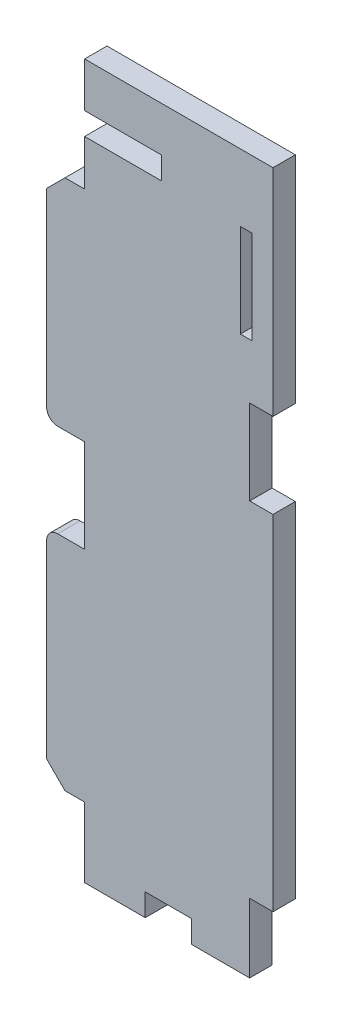
SolidWorks part; units mm, degrees
ref_plane "Front Plane" through (0, 0, 0) normal (0, 0, 1) x (1, 0, 0)
ref_plane "Top Plane" through (0, 0, 0) normal (0, 1, 0) x (1, 0, 0)
ref_plane "Right Plane" through (0, 0, 0) normal (1, 0, 0) x (0, 0, -1)
sketch "Model" plane through (0, 0, 0) normal (0, 0, 1) x (1, 0, 0)
  line L320 (15.6348, 91.059) -> (5.17, 91.059)
  line L321 (27.9538, 88.011) -> (26.379, 88.011)
  line L322 (27.649, 67.818) -> (27.649, 56.261)
  line L323 (30.824, 56.261) -> (27.649, 56.261)
  line L324 (30.824, 9.398) -> (30.824, 56.261)
  line L325 (27.649, 9.398) -> (30.824, 9.398)
  line L326 (27.649, 0) -> (27.649, 9.398)
  line L327 (27.649, 0) -> (19.7242, 0)
  line L328 (19.7242, 0) -> (19.7242, 3.048)
  line L329 (19.7242, 3.048) -> (13.425, 3.048)
  line L330 (13.425, 0) -> (13.425, 3.048)
  line L331 (13.425, 0) -> (5.17, 0)
  line L332 (5.17, 9.398) -> (5.17, 0)
  line L333 (15.6348, 88.011) -> (5.17, 88.011)
  line L334 (15.6348, 91.059) -> (15.6348, 88.011)
  line L335 (5.17, 97.155) -> (30.824, 97.155)
  line L336 (30.824, 67.818) -> (27.649, 67.818)
  line L337 (26.379, 88.011) -> (26.379, 75.311)
  line L338 (26.379, 75.311) -> (27.9538, 75.311)
  line L339 (27.9538, 75.311) -> (27.9538, 88.011)
  line L361 (5.17, 97.155) -> (5.17, 91.059)
  line L362 (30.824, 97.155) -> (30.824, 67.818)
  line L474 (2.5, 81.803) -> (5.17, 81.803)
  line L475 (5.17, 51.9965) -> (1.5, 51.9965)
  line L476 (1.5, 39.3165) -> (5.17, 39.3165)
  line L477 (5.17, 9.51) -> (2.5, 9.51)
  line L478 (0, 53.4965) -> (0, 79.303)
  line L479 (0, 12.01) -> (0, 37.8165)
  line L502 (5.17, 9.51) -> (5.17, 9.398)
  line L503 (5.17, 88.011) -> (5.17, 81.803)
  line L504 (5.17, 51.9965) -> (5.17, 39.3165)
  line L511 (2.5, 81.803) -> (0, 79.303)
  line L512 (0, 12.01) -> (2.5, 9.51)
  arc A72 (1.5, 39.3165) -> (0, 37.8165) centre (1.5, 37.8165) ccw
  arc A73 (0, 53.4965) -> (1.5, 51.9965) centre (1.5, 53.4965) ccw
extrude "Boss-Extrude1" add sketch "Model" along normal blind 3.048
